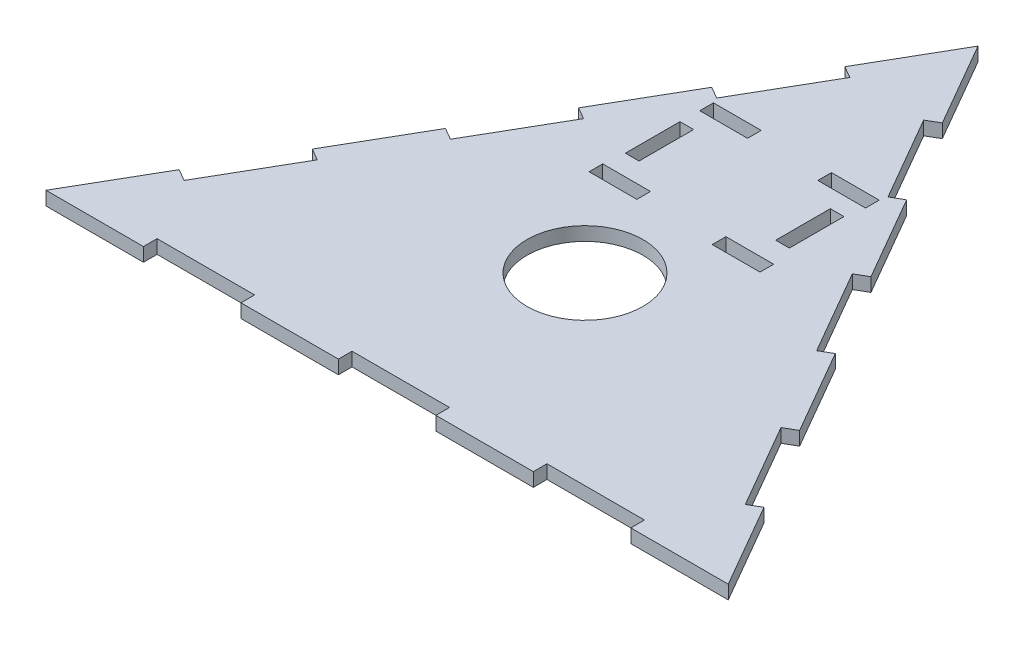
SolidWorks part; units mm, degrees
ref_plane "Front Plane" through (0, 0, 0) normal (0, 0, 1) x (1, 0, 0)
ref_plane "Top Plane" through (0, 0, 0) normal (0, 1, 0) x (1, 0, 0)
ref_plane "Right Plane" through (0, 0, 0) normal (1, 0, 0) x (0, 0, -1)
sketch "Sketch1" plane through (0, 0, 0) normal (0, 1, 0) x (1, 0, 0)
  line L0 (0, 0) -> (-254, 0)
  line L1 (-254, 0) -> (-127, 219.9705)
  line L2 (-127, 219.9705) -> (0, 0)
  dimension "D1" = 254
  dimension "D2" = 254
  dimension "D3" = 254
extrude "Boss-Extrude1" add sketch "Sketch1" along normal blind 5.08
sketch "Sketch2" plane through (0, 0, 0) normal (0.866, 0, -0.5) x (-0.5, 0, -0.866)
  line L0 (0, 0) -> (36.2857, 0) construction
  line L1 (0, 0) -> (254, 0) construction
  line L2 (36.2857, 0) -> (72.5714, 0) construction
  line L3 (72.5714, 0) -> (108.8571, 0) construction
  line L4 (108.8571, 0) -> (145.1429, 0) construction
  line L5 (145.1429, 0) -> (181.4286, 0) construction
  line L6 (181.4286, 0) -> (217.7143, 0) construction
  line L7 (217.7143, 0) -> (254, 0) construction
  line L8 (0, 5.08) -> (254, 5.08) construction
  line L9 (217.7143, 0) -> (181.4286, 0)
  line L10 (217.7143, 0) -> (217.7143, 5.08)
  line L11 (217.7143, 5.08) -> (181.4286, 5.08)
  line L12 (181.4286, 0) -> (181.4286, 5.08)
  line L14 (145.1429, 0) -> (108.8571, 0)
  line L15 (145.1429, 0) -> (145.1429, 5.08)
  line L16 (145.1429, 5.08) -> (108.8571, 5.08)
  line L17 (108.8571, 0) -> (108.8571, 5.08)
  line L18 (72.5714, 0) -> (36.2857, 0)
  line L19 (72.5714, 0) -> (72.5714, 5.08)
  line L20 (72.5714, 5.08) -> (36.2857, 5.08)
  line L21 (36.2857, 0) -> (36.2857, 5.08)
extrude "Cut-Extrude1" cut sketch "Sketch2" against normal blind 5.08
sketch "Sketch3" plane through (-190.5, 0, -109.9852) normal (-0.866, 0, -0.5) x (-0.5, 0, 0.866)
  line L0 (-127, 0) -> (-90.7143, 0)
  line L1 (-127, 0) -> (127, 0) construction
  line L2 (-90.7143, 0) -> (-54.4286, 0)
  line L3 (-54.4286, 0) -> (-18.1429, 0)
  line L4 (-18.1429, 0) -> (18.1429, 0)
  line L5 (18.1429, 0) -> (54.4286, 0)
  line L6 (54.4286, 0) -> (90.7143, 0)
  line L7 (90.7143, 0) -> (127, 0)
  line L8 (-127, 5.08) -> (127, 5.08) construction
  line L9 (-90.7143, 0) -> (-54.4286, 0)
  line L10 (-90.7143, 0) -> (-90.7143, 5.08)
  line L11 (-90.7143, 5.08) -> (-54.4286, 5.08)
  line L12 (-54.4286, 0) -> (-54.4286, 5.08)
  line L14 (-18.1429, 0) -> (18.1429, 0)
  line L15 (-18.1429, 0) -> (-18.1429, 5.08)
  line L16 (-18.1429, 5.08) -> (18.1429, 5.08)
  line L17 (18.1429, 0) -> (18.1429, 5.08)
  line L18 (54.4286, 0) -> (90.7143, 0)
  line L19 (54.4286, 0) -> (54.4286, 5.08)
  line L20 (54.4286, 5.08) -> (90.7143, 5.08)
  line L21 (90.7143, 0) -> (90.7143, 5.08)
  line M8 (-127, 0) -> (127, 0)
  line M10 (127, 5.08) -> (-127, 5.08)
extrude "Cut-Extrude2" cut sketch "Sketch3" against normal blind 5.08 contours L12 L10 M8 M10 | L17 L15 M8 M10 | L21 L19 M8 M10
sketch "Sketch4" plane through (0, 0, 0) normal (0, 0, 1) x (1, 0, 0)
  line L0 (-254, 0) -> (-217.7143, 0)
  line L1 (-254, 0) -> (0, 0) construction
  line L2 (-217.7143, 0) -> (-181.4286, 0)
  line L3 (-181.4286, 0) -> (-145.1429, 0)
  line L4 (-145.1429, 0) -> (-108.8571, 0)
  line L5 (-108.8571, 0) -> (-72.5714, 0)
  line L6 (-72.5714, 0) -> (-36.2857, 0)
  line L7 (-36.2857, 0) -> (0, 0)
  line L8 (-254, 5.08) -> (0, 5.08) construction
  line L9 (-217.7143, 0) -> (-181.4286, 0)
  line L10 (-217.7143, 0) -> (-217.7143, 5.08)
  line L11 (-217.7143, 5.08) -> (-181.4286, 5.08)
  line L12 (-181.4286, 0) -> (-181.4286, 5.08)
  line L14 (-145.1429, 0) -> (-108.8571, 0)
  line L15 (-145.1429, 0) -> (-145.1429, 5.08)
  line L16 (-145.1429, 5.08) -> (-108.8571, 5.08)
  line L17 (-108.8571, 0) -> (-108.8571, 5.08)
  line L18 (-72.5714, 0) -> (-36.2857, 0)
  line L19 (-72.5714, 0) -> (-72.5714, 5.08)
  line L20 (-72.5714, 5.08) -> (-36.2857, 5.08)
  line L21 (-36.2857, 0) -> (-36.2857, 5.08)
  line M11 (-254, 0) -> (0, 0)
  line M13 (0, 5.08) -> (-254, 5.08)
extrude "Cut-Extrude3" cut sketch "Sketch4" against normal blind 5.08 contours L12 L10 M11 M13 | L17 L15 M11 M13 | L21 L19 M11 M13
sketch "Sketch5" plane through (0, 5.08, 0) normal (0, 1, 0) x (1, 0, 0)
  line L0 (-127, 5.08) -> (-127, 73.66)
  line L1 (-108.8571, 5.08) -> (-145.1429, 5.08) construction
  circle A0 centre (-127, 73.66) radius 21.59
  dimension "D2" = 43.18
  dimension "D1" = 68.58
extrude "Cut-Extrude4" cut sketch "Sketch5" against normal blind 5.08
sketch "Sketch6" plane through (0, 10.16, 0) normal (0, 1, 0) x (1, 0, 0)
  line L1 (-157.9459, 152.423) -> (-140.1659, 152.423)
  line L2 (-157.9459, 152.423) -> (-157.9459, 147.343)
  line L3 (-157.9459, 147.343) -> (-140.1659, 147.343)
  line L4 (-140.1659, 152.423) -> (-140.1659, 147.343)
  line L5 (-113.4959, 151.9033) -> (-95.7159, 151.9033)
  line L6 (-113.4959, 151.9033) -> (-113.4959, 146.8233)
  line L7 (-113.4959, 146.8233) -> (-95.7159, 146.8233)
  line L8 (-95.7159, 151.9033) -> (-95.7159, 146.8233)
  line L9 (-96.9859, 140.05) -> (-102.0659, 140.05)
  line L10 (-96.9859, 140.05) -> (-96.9859, 119.73)
  line L11 (-96.9859, 119.73) -> (-102.0659, 119.73)
  line L12 (-102.0659, 140.05) -> (-102.0659, 119.73)
  line L13 (-94.7028, 111.598) -> (-112.4828, 111.598)
  line L14 (-94.7028, 111.598) -> (-94.7028, 106.518)
  line L15 (-94.7028, 106.518) -> (-112.4828, 106.518)
  line L16 (-112.4828, 111.598) -> (-112.4828, 106.518)
  line L17 (-141.0975, 112.1404) -> (-158.8775, 112.1404)
  line L18 (-141.0975, 112.1404) -> (-141.0975, 107.0604)
  line L19 (-141.0975, 107.0604) -> (-158.8775, 107.0604)
  line L20 (-158.8775, 112.1404) -> (-158.8775, 107.0604)
  line L21 (-158.112, 119.8059) -> (-153.032, 119.8059)
  line L22 (-158.112, 119.8059) -> (-158.112, 140.1259)
  line L23 (-158.112, 140.1259) -> (-153.032, 140.1259)
  line L24 (-153.032, 119.8059) -> (-153.032, 140.1259)
extrude "Cut-Extrude5" cut sketch "Sketch6" against normal through all
equation "\"MDFThickness\"= .2in"
equation "\"D1@Boss-Extrude1\"=\"MDFThickness\""
equation "\"D1@Cut-Extrude1\"=\"MDFThickness\""
equation "\"D1@Cut-Extrude2\"=\"MDFThickness\""
equation "\"D1@Cut-Extrude3\"=\"MDFThickness\""
equation "\"D1@Sketch5\"=\"MDFThickness\" *2 + 2.3in"
equation "\"D1@Cut-Extrude4\"=\"MDFThickness\""
